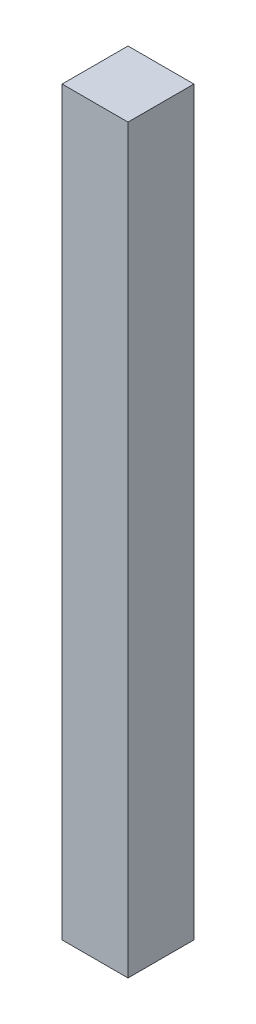
SolidWorks part; units mm, degrees
ref_plane "Спереди" through (0, 0, 0) normal (0, 0, 1) x (1, 0, 0)
ref_plane "Сверху" through (0, 0, 0) normal (0, 1, 0) x (1, 0, 0)
ref_plane "Справа" through (0, 0, 0) normal (1, 0, 0) x (0, 0, -1)
sketch "Эскиз1" plane through (0, 0, 0) normal (0, 1, 0) x (1, 0, 0)
  line L1 (-20, 20) -> (20, 20)
  line L2 (-20, 20) -> (-20, -20)
  line L3 (-20, -20) -> (20, -20)
  line L4 (20, 20) -> (20, -20)
  line L5 (-20, 20) -> (20, -20) construction
  line L6 (-20, -20) -> (20, 20) construction
  point P0 (0, 0)
extrude "Бобышка-Вытянуть1" add sketch "Эскиз1" along normal blind 450
